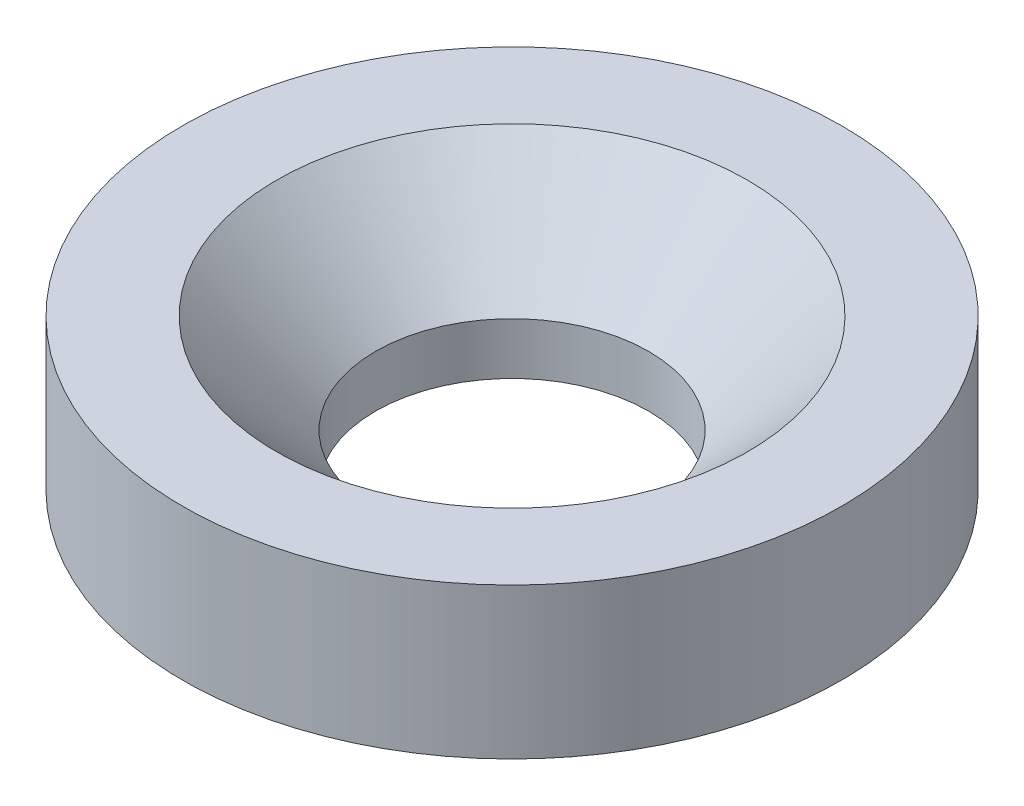
SolidWorks part; units mm, degrees
ref_plane "Front Plane" through (0, 0, 0) normal (0, 0, 1) x (1, 0, 0)
ref_plane "Top Plane" through (0, 0, 0) normal (0, 1, 0) x (1, 0, 0)
ref_plane "Right Plane" through (0, 0, 0) normal (1, 0, 0) x (0, 0, -1)
sketch "Sketch2" plane through (0, 0, 0) normal (0, 0, 1) x (1, 0, 0)
  line L0 (7.25, 0) -> (17.5, 0)
  line L1 (17.5, 0) -> (17.5, 8)
  line L2 (17.5, 8) -> (12.5, 8)
  line L3 (12.5, 8) -> (7.25, 2.75)
  line L4 (7.25, 2.75) -> (7.25, 0)
  line L5 (0, 0) -> (0, 25.1671) construction
  dimension "D1" = 17.5
  dimension "D2" = 12.5
  dimension "D3" = 7.25
  dimension "D4" = 8
  dimension "D5" = 225
revolve "Revolve1" add sketch "Sketch2" angle 360 about L5
